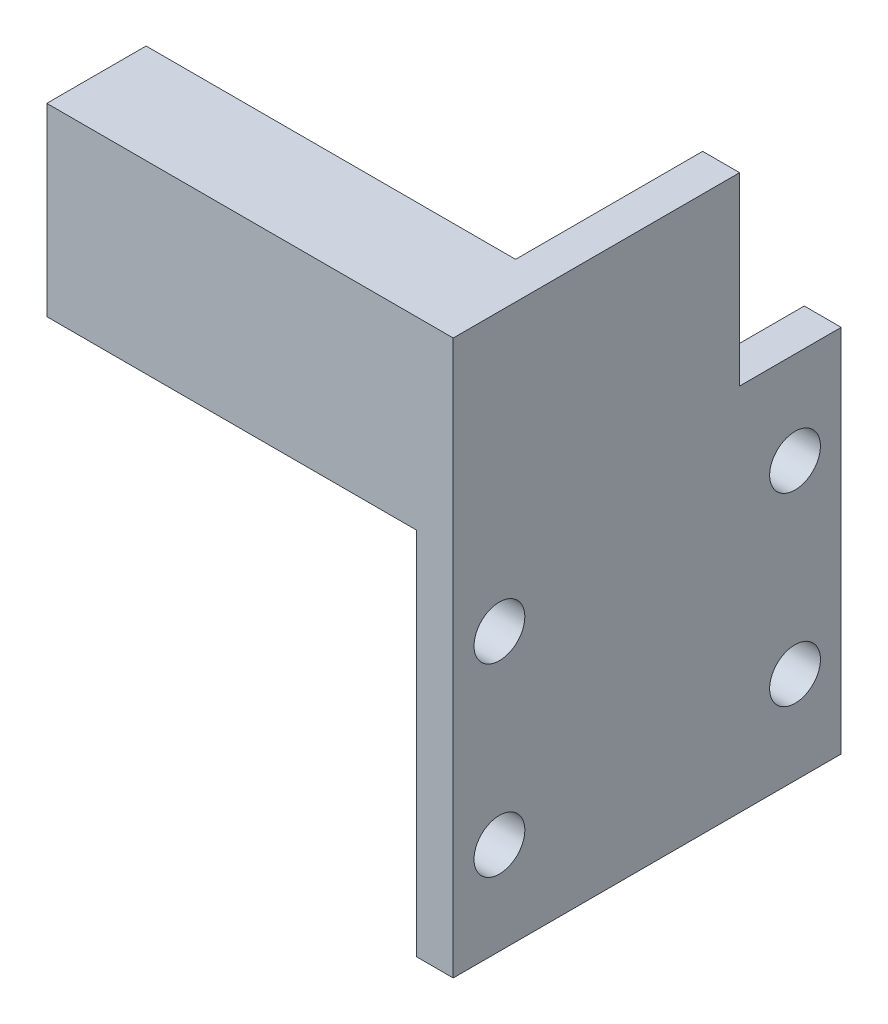
SolidWorks part; units mm, degrees
ref_plane "Front Plane" through (0, 0, 0) normal (0, 0, 1) x (1, 0, 0)
ref_plane "Top Plane" through (0, 0, 0) normal (0, 1, 0) x (1, 0, 0)
ref_plane "Right Plane" through (0, 0, 0) normal (1, 0, 0) x (0, 0, -1)
sketch "Sketch1" plane through (0, 0, 0) normal (1, 0, 0) x (0, 0, -1)
  line L0 (21, 40) -> (21, 0) construction
  line L1 (0, 0) -> (42, 0)
  line L2 (0, 0) -> (0, 40)
  line L3 (0, 40) -> (42, 40)
  line L4 (42, 0) -> (42, 40)
  line L5 (0, 20) -> (42, 20) construction
  circle A0 centre (5, 30) radius 2.75
  circle A2 centre (5, 10) radius 2.75
  circle A3 centre (37, 10) radius 2.75
  circle A4 centre (37, 30) radius 2.75
  point P17 (0, 0)
  dimension "D4" = 5.5
  dimension "D1" = 42
  dimension "D2" = 40
  dimension "D3" = 32
  dimension "D5" = 20
extrude "Boss-Extrude1" add sketch "Sketch1" against normal blind 4
sketch "Sketch3" plane through (0, 40, 0) normal (0, 1, 0) x (1, 0, 0)
  line L3 (-4, 42) -> (-4, 0) construction
  line L4 (-4, 31) -> (-4, 10.75)
  line L5 (-4, 10.75) -> (-44, 10.75)
  line L6 (-44, 10.75) -> (-44, 0)
  line L7 (-44, 0) -> (0, 0)
  line L8 (0, 0) -> (0, 31)
  line L9 (-4, 31) -> (0, 31)
  line L10 (-4, 42) -> (0, 42) construction
  point P8 (0, 0)
  dimension "D1" = 10.75
  dimension "D2" = 40
  dimension "D3" = 11
extrude "Boss-Extrude2" add sketch "Sketch3" along normal blind 20
